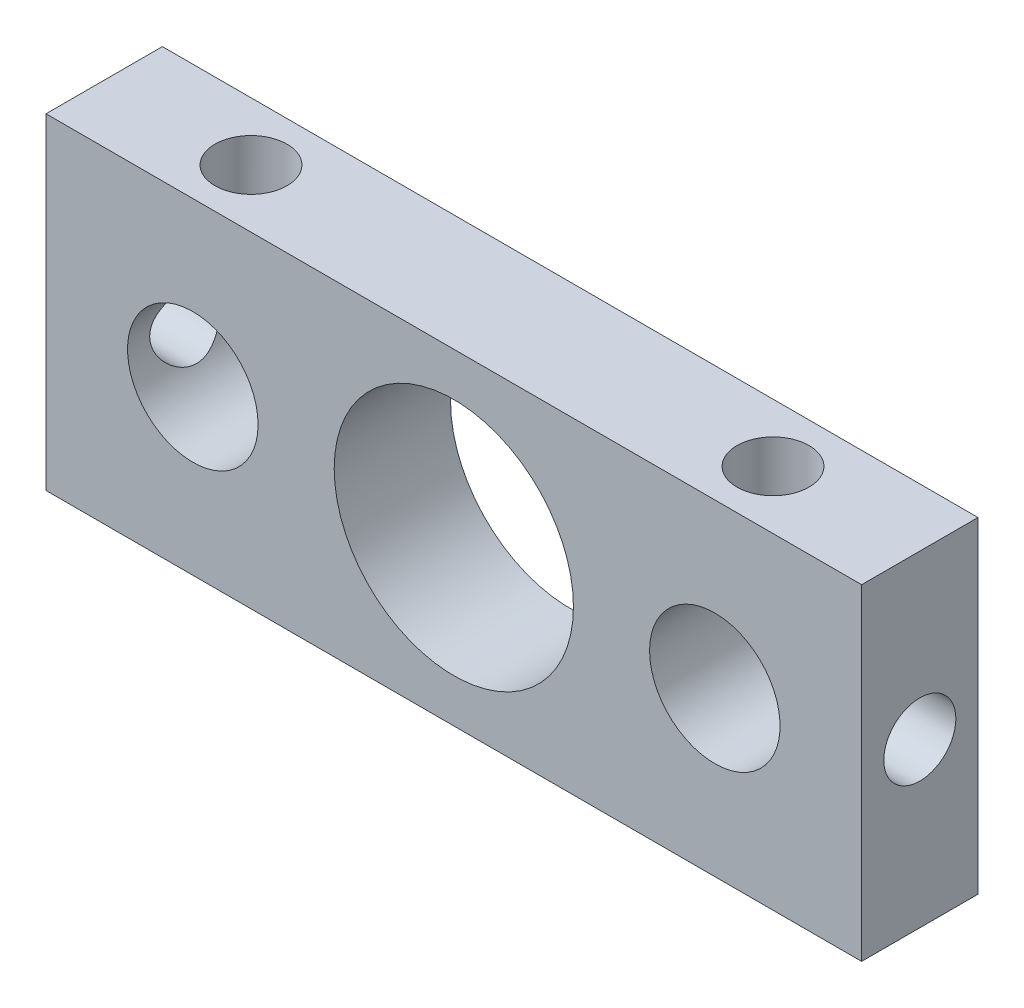
SolidWorks part; units mm, degrees
ref_plane "Plano frontal" through (0, 0, 0) normal (0, 0, 1) x (1, 0, 0)
ref_plane "Plano superior" through (0, 0, 0) normal (0, 1, 0) x (1, 0, 0)
ref_plane "Plano direito" through (0, 0, 0) normal (1, 0, 0) x (0, 0, -1)
sketch "Esboço1" plane through (0, 0, 0) normal (0, 0, 1) x (1, 0, 0)
  line L1 (37.5, -15) -> (-37.5, -15)
  line L2 (37.5, -15) -> (37.5, 15)
  line L3 (37.5, 15) -> (-37.5, 15)
  line L4 (-37.5, -15) -> (-37.5, 15)
  line L5 (37.5, -15) -> (-37.5, 15) construction
  line L6 (37.5, 15) -> (-37.5, -15) construction
  point P0 (0, 0)
  dimension "D1" = 30
  dimension "D2" = 75
extrude "Ressalto-extrusão1" add sketch "Esboço1" along normal blind 10.7
sketch "Esboço2" plane through (0, 0, 10.7) normal (0, 0, 1) x (1, 0, 0)
  line L0 (-35.9706, 0) -> (33.3822, 0) construction
  line L1 (0, -18.6994) -> (0, 18.6101) construction
  circle A0 centre (-24, 0) radius 6
  circle A2 centre (24, 0) radius 6
  dimension "D1" = 12
  dimension "D2" = 24
extrude "Corte-extrusão1" cut sketch "Esboço2" against normal through all
sketch "Esboço7" plane through (0, 0, 10.7) normal (0, 0, 1) x (1, 0, 0)
  circle A0 centre (0, 0) radius 11
  dimension "D1" = 22
extrude "Corte-extrusão6" cut sketch "Esboço7" against normal through all
hole_wizard "Furo roscado para conduíte de 1/4-281" positions "Esboço8" profile "Esboço9" tap size "1/4-28" standard "Helicoil® Inch"
sketch "Esboço8" plane through (0, 15, 0) normal (0, 1, 0) x (1, 0, 0)
  line L0 (-37.5, -10.7) -> (-37.5, 0) construction
  line L1 (37.5, 0) -> (-37.5, 0) construction
  line L2 (0, 8.0368) -> (0, -16.8012) construction
  point P0 (-24, -5.35)
  point P12 (0, 0)
  point P13 (0, 0)
  point P14 (24, -5.35)
  dimension "D1" = 13.5
  dimension "D2" = 5.35
sketch "Esboço9" plane through (-24, 15, 5.35) normal (1, 0, 0) x (0, 0, 1)
  line L0 (0, 0) -> (0, 16.9917)
  line L1 (0, 16.9917) -> (3.3147, 15)
  line L2 (3.3147, 15) -> (3.3147, 0)
  line L5 (3.3147, 0) -> (0, 0)
  line L10 (0, 16.9917) -> (-3.3147, 15) construction
  line L11 (0, -6.35) -> (0, 107.95) construction
  dimension "Tap Drill Dia." = 6.6294
  dimension "Tap Drill Depth" = 15
  dimension "Drill Angle" = 118
cosmetic thread "Rosca de furo1" parameters "D1"=15, "D2"=7.6073
cosmetic thread "Rosca de furo2" parameters "D1"=15, "D2"=7.6073
hole_wizard "Furo roscado para conduíte de 1/4-282" positions "Esboço10" profile "Esboço11" tap size "1/4-28" standard "Helicoil® Inch"
sketch "Esboço10" plane through (-37.5, 0, 0) normal (-1, 0, 0) x (0, 0, 1)
  line L0 (0, 15) -> (0, -15) construction
  line L1 (10.7, 15) -> (0, 15) construction
  point P0 (5.35, 0)
  dimension "D1" = 5.35
  dimension "D2" = 15
sketch "Esboço11" plane through (-37.5, 0, 5.35) normal (0, 1, 0) x (0, 0, 1)
  line L0 (0, 0) -> (0, 16.9917)
  line L1 (0, 16.9917) -> (3.3147, 15)
  line L2 (3.3147, 15) -> (3.3147, 0)
  line L5 (3.3147, 0) -> (0, 0)
  line L10 (0, 16.9917) -> (-3.3147, 15) construction
  line L11 (0, -6.35) -> (0, 107.95) construction
  dimension "Tap Drill Dia." = 6.6294
  dimension "Tap Drill Depth" = 15
  dimension "Drill Angle" = 118
cosmetic thread "Rosca de furo3" parameters "D1"=15, "D2"=7.6073
hole_wizard "Furo roscado para conduíte de 1/4-283" positions "Esboço12" profile "Esboço13" tap size "1/4-28" standard "Helicoil® Inch"
sketch "Esboço12" plane through (37.5, 0, 0) normal (1, 0, 0) x (0, 0, -1)
  line L0 (-10.7, -15) -> (-10.7, 15) construction
  line L1 (-10.7, -15) -> (0, -15) construction
  point P0 (-5.35, 0)
  dimension "D1" = 5.35
  dimension "D2" = 15
sketch "Esboço13" plane through (37.5, 0, 5.35) normal (0, 1, 0) x (0, 0, -1)
  line L0 (0, 0) -> (0, 16.9917)
  line L1 (0, 16.9917) -> (3.3147, 15)
  line L2 (3.3147, 15) -> (3.3147, 0)
  line L5 (3.3147, 0) -> (0, 0)
  line L10 (0, 16.9917) -> (-3.3147, 15) construction
  line L11 (0, -6.35) -> (0, 107.95) construction
  dimension "Tap Drill Dia." = 6.6294
  dimension "Tap Drill Depth" = 15
  dimension "Drill Angle" = 118
cosmetic thread "Rosca de furo4" parameters "D1"=15, "D2"=7.6073
hole_wizard "Furo roscado para conduíte de 1/4-284" positions "Esboço14" profile "Esboço15" tap size "1/4-28" standard "Helicoil® Inch"
sketch "Esboço14" plane through (0, -15, 0) normal (0, -1, 0) x (-1, 0, 0)
  line L0 (37.5, 0) -> (-37.5, 0) construction
  line L1 (37.5, -10.7) -> (37.5, 0) construction
  line L2 (0, 8.3834) -> (0, -19.7161) construction
  point P0 (15, -5.35)
  point P12 (0, 0)
  point P13 (-15, -5.35)
  dimension "D1" = 5.35
  dimension "D2" = 22.5
sketch "Esboço15" plane through (-15, -15, 5.35) normal (1, 0, 0) x (0, 0, -1)
  line L0 (0, 0) -> (0, 13.9917)
  line L1 (0, 13.9917) -> (3.3147, 12)
  line L2 (3.3147, 12) -> (3.3147, 0)
  line L5 (3.3147, 0) -> (0, 0)
  line L10 (0, 13.9917) -> (-3.3147, 12) construction
  line L11 (0, -6.35) -> (0, 107.95) construction
  dimension "Tap Drill Dia." = 6.6294
  dimension "Tap Drill Depth" = 12
  dimension "Drill Angle" = 118
cosmetic thread "Rosca de furo5" parameters "D1"=12, "D2"=7.6073
cosmetic thread "Rosca de furo6" parameters "D1"=12, "D2"=7.6073
